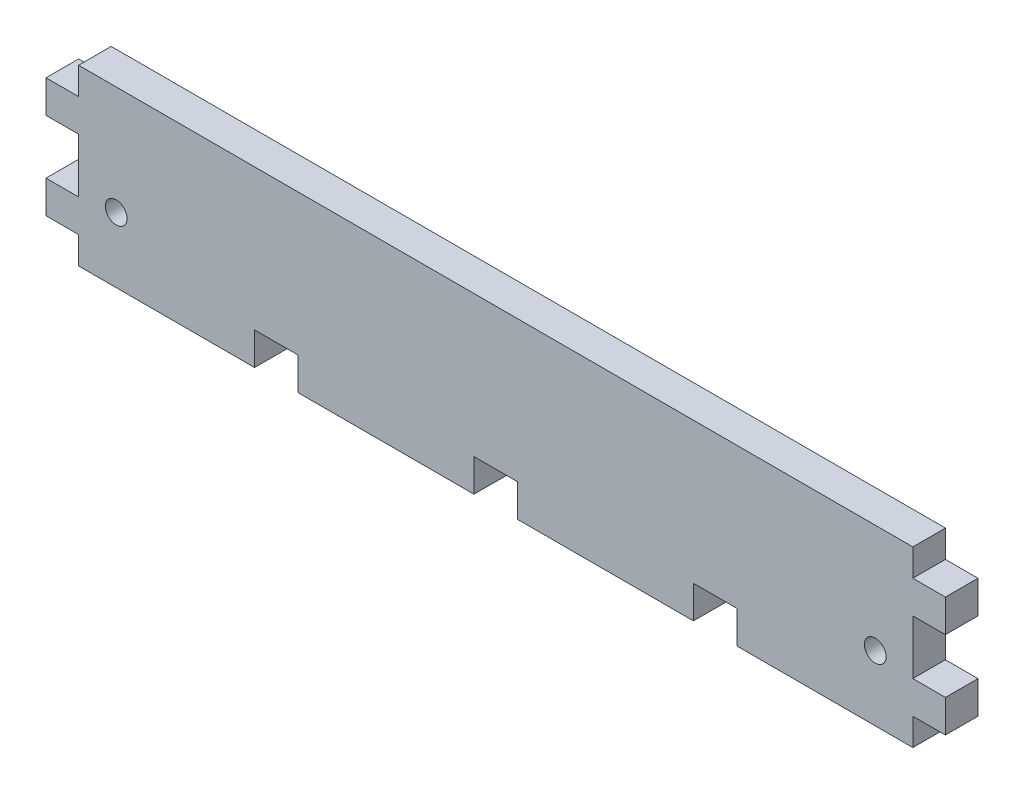
SolidWorks part; units mm, degrees
ref_plane "Front Plane" through (0, 0, 0) normal (0, 0, 1) x (1, 0, 0)
ref_plane "Top Plane" through (0, 0, 0) normal (0, 1, 0) x (1, 0, 0)
ref_plane "Right Plane" through (0, 0, 0) normal (1, 0, 0) x (0, 0, -1)
sketch "Sketch1" plane through (0, 0, 0) normal (0, 0, 1) x (1, 0, 0)
  line L0 (0, 0) -> (0, 12.5)
  line L1 (0, 12.5) -> (-15, 12.5)
  line L2 (-15, 12.5) -> (-15, 27.5)
  line L3 (-15, 27.5) -> (0, 27.5)
  line L4 (0, 27.5) -> (0, 52.5)
  line L5 (0, 52.5) -> (-15, 52.5)
  line L6 (-15, 52.5) -> (-15, 67.5)
  line L7 (-15, 67.5) -> (0, 67.5)
  line L8 (0, 67.5) -> (0, 80)
  line L9 (0, 80) -> (384, 80)
  line L10 (384, 80) -> (384, 67.5)
  line L11 (384, 67.5) -> (399, 67.5)
  line L12 (399, 67.5) -> (399, 52.5)
  line L13 (399, 52.5) -> (384, 52.5)
  line L14 (384, 52.5) -> (384, 27.5)
  line L15 (384, 27.5) -> (399, 27.5)
  line L16 (399, 27.5) -> (399, 12.5)
  line L17 (399, 12.5) -> (384, 12.5)
  line L18 (384, 12.5) -> (384, 0)
  line L19 (384, 0) -> (303, 0)
  line L20 (303, 0) -> (303, 15)
  line L21 (303, 15) -> (283, 15)
  line L22 (283, 15) -> (283, 0)
  line L23 (283, 0) -> (202, 0)
  line L24 (202, 0) -> (202, 15)
  line L25 (202, 15) -> (182, 15)
  line L26 (182, 15) -> (182, 0)
  line L27 (182, 0) -> (101, 0)
  line L28 (101, 0) -> (101, 15)
  line L29 (101, 15) -> (81, 15)
  line L30 (81, 15) -> (81, 0)
  line L31 (81, 0) -> (0, 0)
  line L32 (192, 80) -> (192, 64.512) construction
  circle A0 centre (17.3, 30) radius 5
  circle A1 centre (366.7, 30) radius 5
  dimension "D31" = 10
  dimension "D1" = 12.5
  dimension "D2" = 15
  dimension "D3" = 15
  dimension "D4" = 25
  dimension "D5" = 15
  dimension "D6" = 15
  dimension "D7" = 15
  dimension "D8" = 12.5
  dimension "D9" = 384
  dimension "D10" = 12.5
  dimension "D11" = 15
  dimension "D12" = 15
  dimension "D13" = 15
  dimension "D14" = 25
  dimension "D15" = 15
  dimension "D16" = 15
  dimension "D17" = 15
  dimension "D18" = 12.5
  dimension "D19" = 81
  dimension "D20" = 15
  dimension "D21" = 20
  dimension "D22" = 15
  dimension "D23" = 81
  dimension "D24" = 81
  dimension "D25" = 81
  dimension "D26" = 20
  dimension "D27" = 15
  dimension "D28" = 15
  dimension "D29" = 30
  dimension "D30" = 17.3
extrude "Boss-Extrude1" add sketch "Sketch1" along normal blind 15
